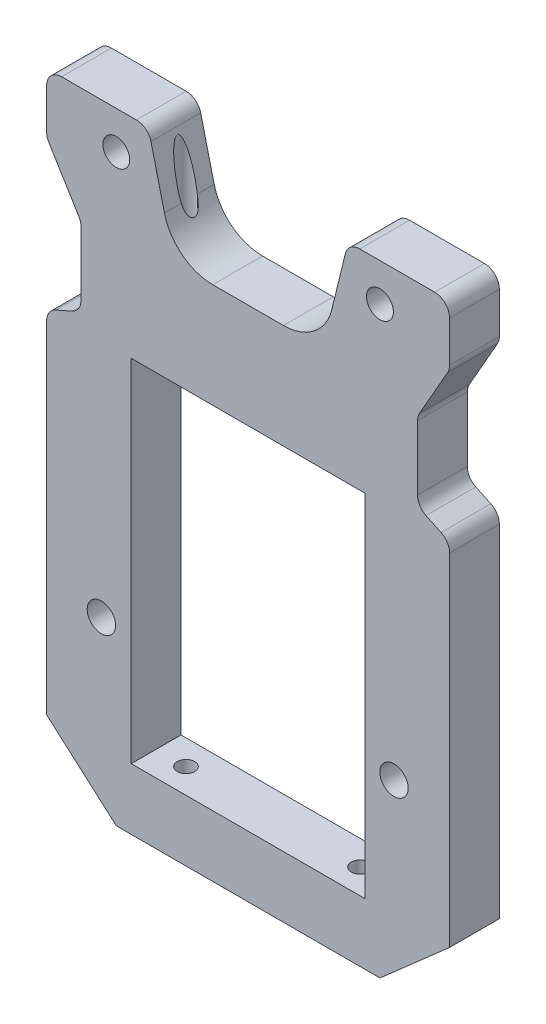
SolidWorks part; units mm, degrees
ref_plane "Спереди" through (0, 0, 0) normal (0, 0, 1) x (1, 0, 0)
ref_plane "Сверху" through (0, 0, 0) normal (0, 1, 0) x (1, 0, 0)
ref_plane "Справа" through (0, 0, 0) normal (1, 0, 0) x (0, 0, -1)
sketch "Эскиз2" plane through (0, 0, 0) normal (0, 0, 1) x (1, 0, 0)
  line L0 (0, 100.0976) -> (20.3937, 100.0976)
  line L1 (80.9803, 100.0976) -> (80.9803, 88.0976)
  line L2 (20.3937, 100.0976) -> (23.67, 86.719)
  line L3 (30.6791, 58.0976) -> (50.3012, 58.0976)
  line L4 (0, 58.0976) -> (17, 58.0976)
  line L5 (0, 88.0976) -> (0, 100.0976)
  line L6 (17, 58.0976) -> (17, -12.4671)
  line L7 (0, 17.5329) -> (0, 5.2193)
  line L8 (0, -12.4671) -> (14, -24.7807)
  line L9 (80.9803, 5.2193) -> (80.9803, 17.5329)
  line L10 (60.5866, 100.0976) -> (80.9803, 100.0976)
  line L11 (60.5866, 100.0976) -> (57.3103, 86.719)
  line L12 (0, -12.4671) -> (17, -12.4671)
  line L13 (0, 17.5329) -> (0, 58.0976)
  line L14 (80.9803, 58.0976) -> (80.9803, 17.5329)
  line L15 (80.9803, -12.4671) -> (63.9803, -12.4671)
  line L16 (33.383, 79.0976) -> (47.5973, 79.0976)
  line L17 (0, 58.0976) -> (17, 58.0976)
  line L18 (63.9803, -12.4671) -> (63.9803, 58.0976)
  line L19 (17, -12.4671) -> (63.9803, -12.4671)
  line L20 (0, 88.0976) -> (6.8958, 76.8113)
  line L21 (6.8958, 76.8113) -> (6.8958, 61.1479)
  line L22 (6.8958, 61.1479) -> (0, 58.0976)
  line L23 (66.9803, -907.5) -> (66.9803, 49092.5) construction
  line L24 (0, 58.0976) -> (80.9803, 58.0976)
  line L25 (80.9803, -12.4671) -> (66.9803, -24.7807)
  line L26 (80.9803, 88.0976) -> (74.5394, 76.8113)
  line L27 (74.5394, 76.8113) -> (74.5394, 61.1479)
  line L28 (14, -907.5) -> (14, 49092.5) construction
  line L29 (0, 5.2193) -> (0, -12.4671)
  line L30 (80.9803, -12.4671) -> (80.9803, 5.2193)
  line L31 (14, -24.7807) -> (66.9803, -24.7807)
  line L32 (14, 58.0976) -> (17, 58.0976)
  line L33 (74.5394, 61.1479) -> (80.9803, 58.0976)
  line L34 (66.9803, 58.0976) -> (63.9803, 58.0976)
  circle A0 centre (14, 92.5) radius 2.7
  circle A1 centre (66.9803, 92.5) radius 2.7
  circle A2 centre (11, 10) radius 2.85
  circle A3 centre (69.8085, 11.0646) radius 2.85
  arc A4 (57.3103, 86.719) -> (47.5973, 79.0976) centre (47.5973, 89.0976) cw
  arc A5 (23.67, 86.719) -> (33.383, 79.0976) centre (33.383, 89.0976) ccw
  dimension "D1" = 10
extrude "Бобышка-Вытянуть1" add sketch "Эскиз2" along normal blind 10
sketch "Эскиз4" plane through (0, 100.0976, 0) normal (0, 1, 0) x (1, 0, 0)
  line L1 (0, -10) -> (0, -5)
  line L4 (0, -5) -> (23, -5)
  line L6 (40.4901, -5) -> (40.4901, 4.3225)
  line L8 (0, 0) -> (80.9803, 0)
  line L9 (0, 0) -> (0, -10)
  line L11 (80.9803, 0) -> (80.9803, -10)
  circle A0 centre (23, -5) radius 1.75
  circle A1 centre (57.9803, -5) radius 1.75
  circle A2 centre (23, -5) radius 1.75
  circle A3 centre (57.9803, -5) radius 1.75
extrude "Вырез-Вытянуть1" cut sketch "Эскиз4" against normal through all
fillet "Скругление1" radius 3 12 edges at (20.3937, 100.0976, 5) (60.5866, 100.0976, 5) (80.9803, 100.0976, 5) (0, 100.0976, 5) (0, 58.0976, 5) (6.8958, 61.1479, 5) (0, 88.0976, 5) (6.8958, 76.8113, 5) (80.9803, 88.0976, 5) (80.9803, 58.0976, 5) (74.5394, 61.1479, 5) (74.5394, 76.8113, 5)
